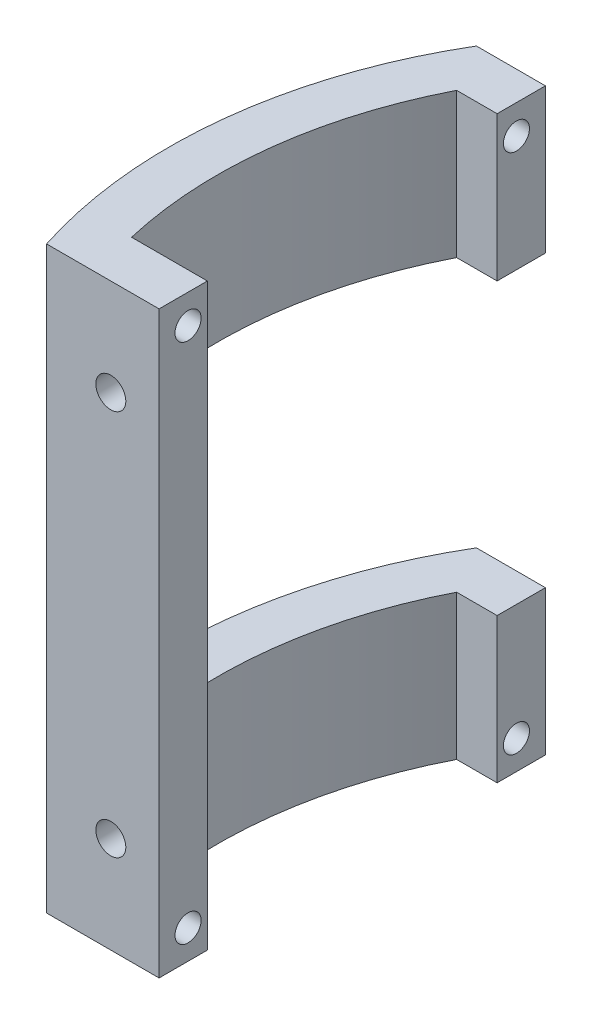
SolidWorks part; units mm, degrees
ref_plane "Front Plane" through (0, 0, 0) normal (0, 0, 1) x (1, 0, 0)
ref_plane "Top Plane" through (0, 0, 0) normal (0, 1, 0) x (1, 0, 0)
ref_plane "Right Plane" through (0, 0, 0) normal (1, 0, 0) x (0, 0, -1)
sketch "Sketch1" plane through (0, 0, 0) normal (0, 1, 0) x (1, 0, 0)
  line L0 (-46.6476, -15) -> (46.6476, -15)
  line L1 (-43.2666, -23) -> (43.2666, -23)
  line L2 (-55, 0) -> (55, 0) construction
  line L3 (-42.1426, 25) -> (42.1426, 25)
  line L4 (-39.1918, 20) -> (44.7325, 20)
  line L5 (-42.8486, -10) -> (47.9687, -10)
  line L6 (-35, 25) -> (-35, -15)
  line L7 (0, -55) -> (0, 55) construction
  circle A0 centre (0, 0) radius 49
  arc A1 (-39.1918, 20) -> (-42.8486, -10) centre (0, 0) ccw
  arc A2 (-41.3642, -15) -> (-36.2077, 25) centre (0, 0) ccw
  dimension "D1" = 98
  dimension "D2" = 88
  dimension "D3" = 8
  dimension "D4" = 15
  dimension "D5" = 40
  dimension "D6" = 5
  dimension "D7" = 5
  dimension "D8" = 35
extrude "Boss-Extrude1" add sketch "Sketch1" along normal blind 60 contours A1 L4 L6 L3 A0 L0 L5
sketch "Sketch2" plane through (0, 0, 10) normal (0, 0, -1) x (-1, 0, 0)
  line L0 (42.8486, 60) -> (35, 60) construction
  circle A0 centre (39.9976, 50) radius 1.55
  circle A1 centre (39.9976, 10) radius 1.55
  dimension "D1" = 6.65
  dimension "D2" = 10
  dimension "D3" = 2
extrude "Cut-Extrude1" cut sketch "Sketch2" against normal through all
sketch "Sketch4" plane through (-35, 0, 0) normal (1, 0, 0) x (0, 0, -1)
  line L0 (25, 45) -> (-10, 45)
  line L2 (25, 60) -> (25, 0) construction
  line L3 (-10, 60) -> (-10, 0) construction
  line L4 (-10, 45) -> (-10, 15)
  line L5 (-10, 15) -> (25, 15)
  line L6 (25, 15) -> (25, 45)
  line L7 (20, 60) -> (-10, 60) construction
  point P8 (25, 30)
  dimension "D1" = 30
  dimension "D2" = 30
extrude "Cut-Extrude3" cut sketch "Sketch4" against normal through all
sketch "Sketch5" plane through (-35, 0, 0) normal (1, 0, 0) x (0, 0, -1)
  line L0 (20, 60) -> (-10, 60) construction
  line L1 (-12, 3) -> (22, 3)
  line L2 (-12, 3) -> (-12, 57)
  line L3 (-12, 57) -> (22, 57)
  line L4 (22, 3) -> (22, 57)
  line L5 (-12, 3) -> (22, 57) construction
  line L6 (-12, 57) -> (22, 3) construction
  line L7 (-15, 60) -> (-15, 0) construction
  circle A0 centre (-12, 57) radius 1.35
  circle A1 centre (22, 57) radius 1.35
  circle A2 centre (-12, 3) radius 1.35
  circle A3 centre (22, 3) radius 1.35
  point P0 (5, 30)
  dimension "D1" = 54
  dimension "D2" = 34
  dimension "D3" = 30
  dimension "D4" = 20
extrude "Cut-Extrude4" cut sketch "Sketch5" against normal blind 5 contours A0 | A1 | A2 | A3
